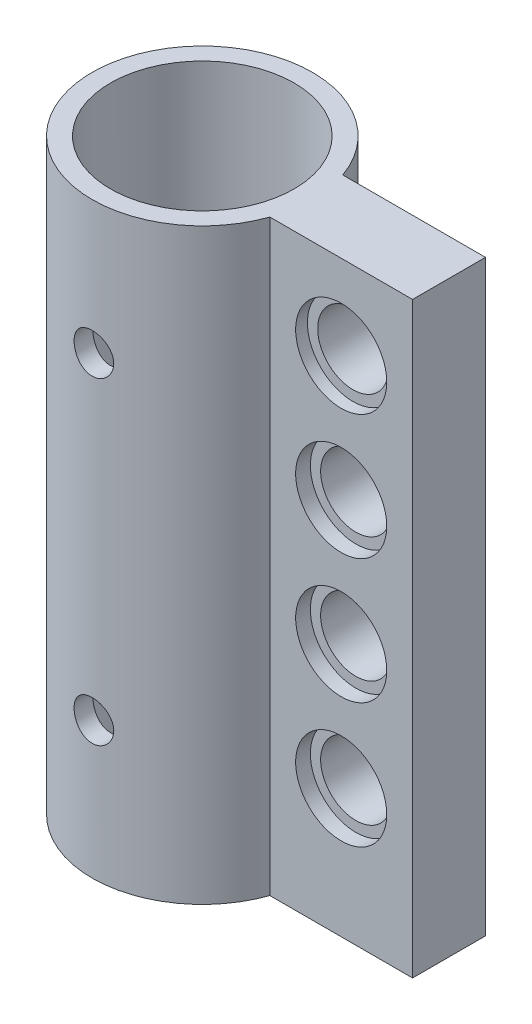
SolidWorks part; units mm, degrees
ref_plane "Front Plane" through (0, 0, 0) normal (0, 0, 1) x (1, 0, 0)
ref_plane "Top Plane" through (0, 0, 0) normal (0, 1, 0) x (1, 0, 0)
ref_plane "Right Plane" through (0, 0, 0) normal (1, 0, 0) x (0, 0, -1)
sketch "Sketch1" plane through (0, 0, 0) normal (0, 1, 0) x (1, 0, 0)
  line L0 (-0.4054, 0) -> (40.2993, 0) construction
  line L1 (7.0776, 2.4813) -> (16.7933, 2.4813)
  line L4 (16.7933, 2.4813) -> (16.7933, 0.4534)
  line L7 (16.7933, -2.4813) -> (16.7933, -0.4534)
  line L8 (7.0776, -2.4813) -> (16.7933, -2.4813)
  line L9 (16.7933, 0.4534) -> (16.7933, -0.4534)
  arc A0 (7.0776, 2.4813) -> (7.0776, -2.4813) centre (0, 0) ccw
  arc A1 (6.1092, 1.319) -> (6.1092, -1.319) centre (0, 0) ccw
  arc A2 (6.1092, 1.319) -> (6.1092, -1.319) centre (0, 0) cw
  dimension "D1" = 12.5
  dimension "D2" = 15
extrude "Boss-Extrude1" add sketch "Sketch1" along normal blind 20
sketch "Sketch2" plane through (0, 0, 2.4813) normal (0, 0, 1) x (1, 0, 0)
  line L0 (11.9355, 20) -> (11.9355, 0) construction
  line L1 (7.0776, 20) -> (16.7933, 20) construction
  line L2 (7.0776, 0) -> (16.7933, 0) construction
  line L3 (7.0776, 10) -> (16.7933, 10) construction
  line L4 (7.0776, 20) -> (7.0776, 0) construction
  line L5 (16.7933, 20) -> (16.7933, 0) construction
  circle A0 centre (11.9355, 14.25) radius 2.4
  circle A1 centre (11.9355, 5.75) radius 2.4
  dimension "D1" = 4.8
  dimension "D2" = 4.25
extrude "Cut-Extrude2" cut sketch "Sketch2" against normal through all
sketch "Sketch3" plane through (0, 0, 2.4813) normal (0, 0, 1) x (1, 0, 0)
  circle A0 centre (11.9355, 14.25) radius 3.1
  circle A1 centre (11.9355, 5.75) radius 3.1
extrude "Cut-Extrude3" cut sketch "Sketch3" against normal blind 0.8 contours A1 | A0
mirror "Mirror1" [suppressed] about plane through (0, 0, 0) normal (0, 0, 1)
ref_plane "Plane1" through (-7.5, 0, 0) normal (-1, 0, 0) x (0, 0, 1)
sketch "Sketch4" plane through (-7.5, 0, 0) normal (-1, 0, 0) x (0, 0, 1)
  line L0 (0, -11) -> (0, 11) construction
  circle A0 centre (0, 10.4435) radius 1.35
  dimension "D1" = 2.7
extrude "Cut-Extrude4" cut sketch "Sketch4" against normal up to next contours A0
mirror "Mirror2" about plane through (0, 0, 0) normal (0, 1, 0) of "Cut-Extrude4", "Boss-Extrude1", "Mirror1"
ref_plane "Plane2" through (0, 0, 7.5) normal (0, 0, 1) x (1, 0, 0)
sketch "Sketch5" plane through (0, 0, 7.5) normal (0, 0, 1) x (1, 0, 0)
  line L0 (0, -8.25) -> (0, 8.25) construction
  circle A0 centre (0, 10.9389) radius 1.35
  circle A1 centre (0, -10.7024) radius 1.35
  dimension "D1" = 2.7
  dimension "D2" = 2.7
extrude "Cut-Extrude5" cut sketch "Sketch5" against normal blind 5
sketch "Sketch6" plane through (0, 0, 2.4813) normal (0, 0, 1) x (1, 0, 0)
  circle A0 centre (11.9355, -11.25) radius 2.4
  circle A1 centre (11.9355, -2.75) radius 2.4
extrude "Cut-Extrude6" cut sketch "Sketch6" against normal blind 5
sketch "Sketch7" plane through (0, 0, 2.4813) normal (0, 0, 1) x (1, 0, 0)
  circle A0 centre (11.9355, 5.75) radius 3.1 construction
  circle A1 centre (11.9355, 5.75) radius 3.1
  circle A2 centre (11.9355, -2.75) radius 3.1
  circle A3 centre (11.9355, -11.25) radius 3.1
extrude "Cut-Extrude7" cut sketch "Sketch7" against normal blind 1
